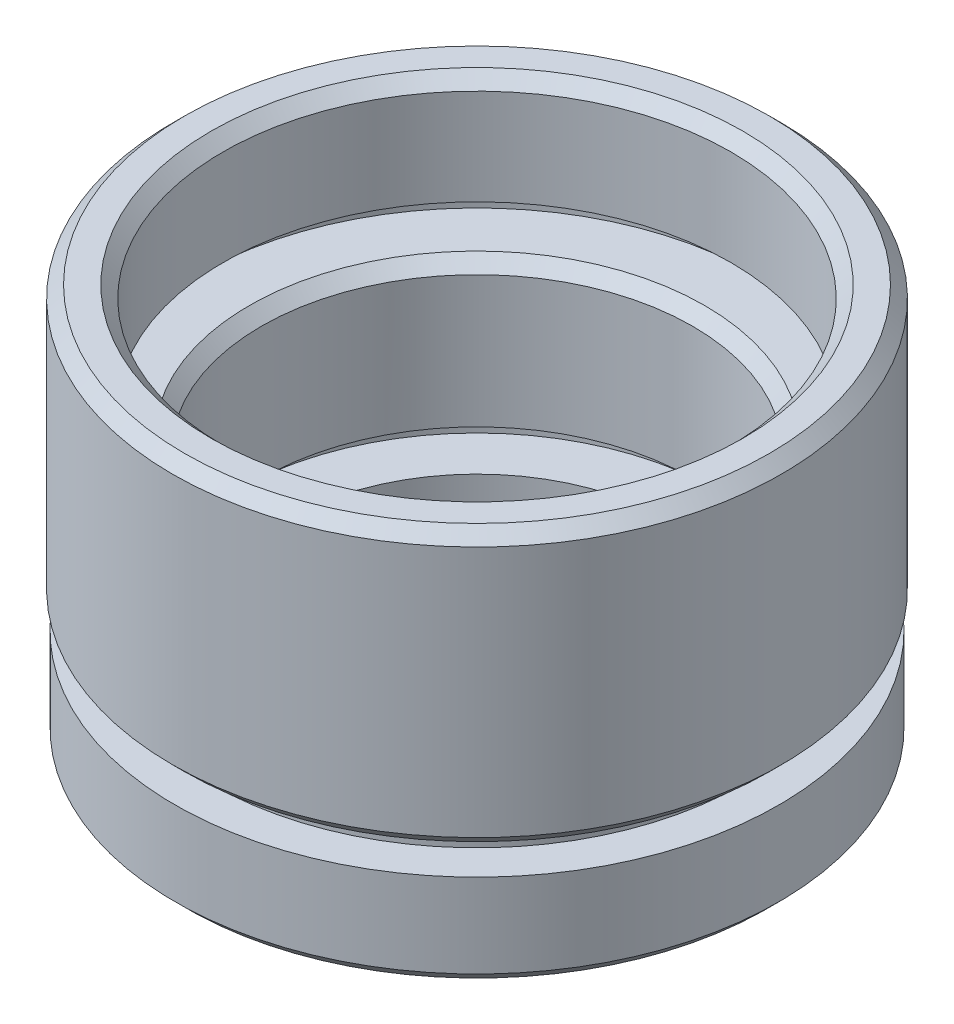
SolidWorks part; units mm, degrees
ref_plane "前视基准面" through (0, 0, 0) normal (0, 0, 1) x (1, 0, 0)
ref_plane "上视基准面" through (0, 0, 0) normal (0, 1, 0) x (1, 0, 0)
ref_plane "右视基准面" through (0, 0, 0) normal (1, 0, 0) x (0, 0, -1)
sketch "草图1" plane through (0, 0, 0) normal (0, 0, 1) x (1, 0, 0)
  line L0 (0, 0) -> (0, 51.3875) construction
  line L1 (7.25, 0) -> (7.25, 2)
  line L2 (7.25, 2) -> (8, 2)
  line L3 (8, 2) -> (8, 4)
  line L4 (8, 4) -> (10.1, 4)
  line L5 (10.1, 4) -> (10.1, 5)
  line L6 (10.1, 5) -> (9, 5)
  line L7 (9, 5) -> (9, 11)
  line L8 (9, 11) -> (11.7, 11)
  line L9 (7.25, 0) -> (12.1, 0)
  line L10 (11.7, 11) -> (11.7, 12)
  line L11 (11.7, 12) -> (10.6, 12)
  line L12 (10.6, 12) -> (10.6, 16.5)
  line L13 (10.6, 16.5) -> (12.2, 16.5)
  line L14 (0, 0) -> (5.8539, 0) construction
  line L15 (12.6, 0.5) -> (12.6, 4)
  line L16 (12.6, 4) -> (11.1, 4)
  line L17 (11.1, 4) -> (11.1, 5)
  line L18 (11.1, 5) -> (12.2, 5)
  line L19 (12.7, 5.5) -> (12.7, 16)
  line L20 (12.1, 0) -> (12.6, 0.5)
  line L21 (12.2, 5) -> (12.7, 5.5)
  line L22 (12.7, 16) -> (12.2, 16.5)
  point P13 (12.6, 0)
  point P22 (12.7, 5)
  point P24 (12.7, 16.5)
  dimension "D1" = 7.25
  dimension "D2" = 2
  dimension "D3" = 8
  dimension "D4" = 2
  dimension "D5" = 10.1
  dimension "D6" = 1
  dimension "D7" = 9
  dimension "D8" = 1
  dimension "D9" = 11.7
  dimension "D10" = 5.5
  dimension "D11" = 16.5
  dimension "D12" = 10.6
  dimension "D13" = 12.6
  dimension "D14" = 1
  dimension "D15" = 0.5
  dimension "D16" = 11.1
  dimension "D17" = 12.7
  dimension "D18" = 0.5
  dimension "D19" = 45
  dimension "D20" = 45
  dimension "D21" = 0.5
  dimension "D22" = 45
  dimension "D23" = 5
revolve "旋转1" add sketch "草图1" angle 360 about L0
cosmetic thread "装饰螺纹线1"
cosmetic thread "装饰螺纹线2"
cosmetic thread "装饰螺纹线3"
chamfer "倒角1" distance 0.5 angle 45 2 edges at (0, 11, -9) (0, 16.5, -10.6)
